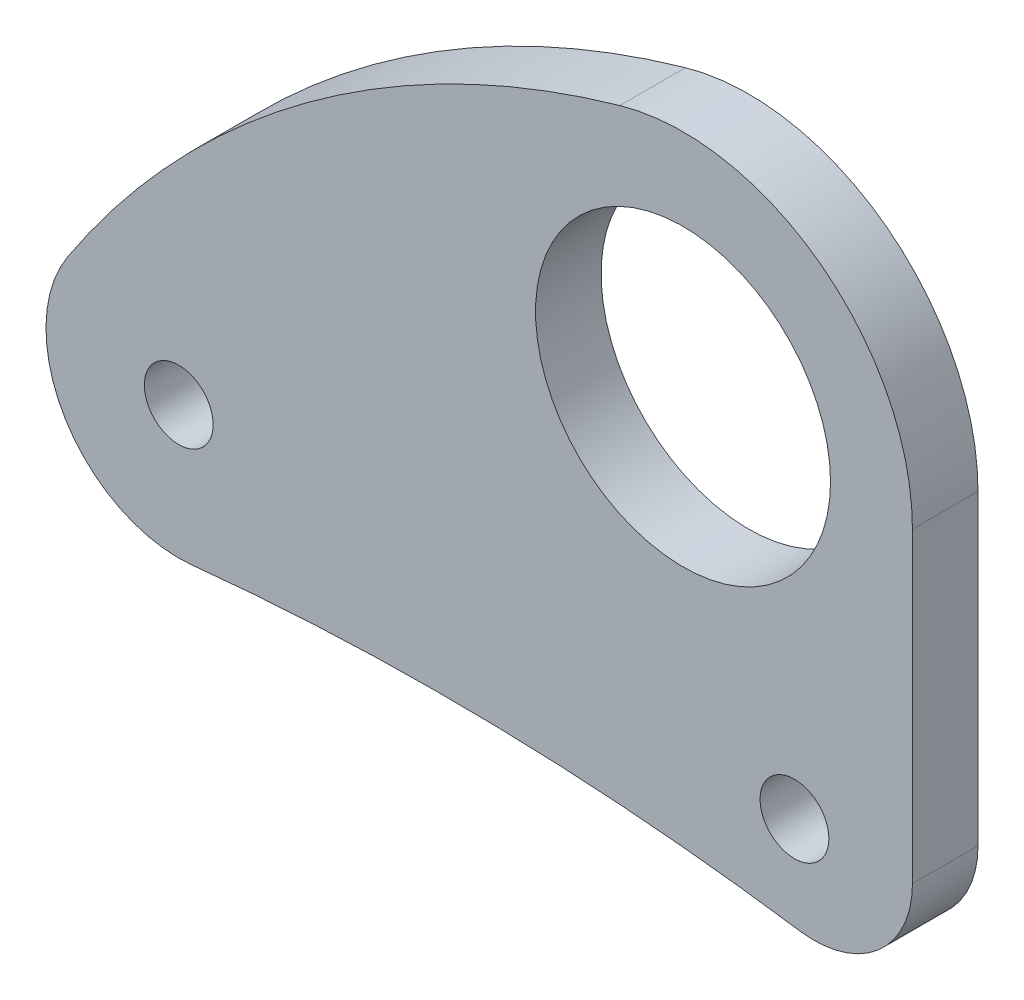
SolidWorks part; units mm, degrees
material "XC38"
ref_plane "Face" through (0, 0, 0) normal (0, 0, 1) x (1, 0, 0)
ref_plane "Dessus" through (0, 0, 0) normal (0, 1, 0) x (1, 0, 0)
ref_plane "Droite" through (0, 0, 0) normal (1, 0, 0) x (0, 0, -1)
sketch "Esquisse1" plane through (0, 0, 0) normal (0, 0, 1) x (1, 0, 0)
  line L0 (14, 0) -> (14, -18.7357)
  line L1 (3.0448, -8.4693) -> (6.0896, -16.9386) construction
  line L2 (-28.6797, -15.9905) -> (4.7071, -18.7423) construction
  line L3 (-28.9049, -14.8579) -> (-8.0044, -4.1145) construction
  line L4 (-30.4935, -23.9256) -> (8.23, -24.7419) construction
  circle A0 centre (0, 0) radius 9
  arc A1 (14, 0) -> (-3.8545, 13.4589) centre (0, 0) ccw
  arc A2 (-3.8545, 13.4589) -> (-37.5518, -11.3849) centre (12.6648, -44.2222) ccw
  circle A3 centre (6.8, -18.9148) radius 2.1
  circle A4 centre (-30.7726, -15.818) radius 2.1
  arc A5 (-29.9443, -23.8755) -> (7.1306, -24.6724) centre (-14.6055, -173.0892) cw
  arc A6 (14, -18.7357) -> (7.1306, -24.6724) centre (8, -18.7357) cw
  arc A7 (-37.5518, -11.3849) -> (-29.9443, -23.8755) centre (-30.7726, -15.818) ccw
  dimension "D1" = 18
  dimension "D2" = 5
  dimension "D3" = 4.2
  dimension "D7" = 6
  dimension "D8" = 6
  dimension "D11" = 60
  dimension "D12" = 150
  dimension "D4" = 9
  dimension "D5" = 33.5
  dimension "D6" = 23.5
  dimension "D9" = 7.2
  dimension "D10" = 6
extrude "Boss.-Extru.1" add sketch "Esquisse1" along normal blind 4
